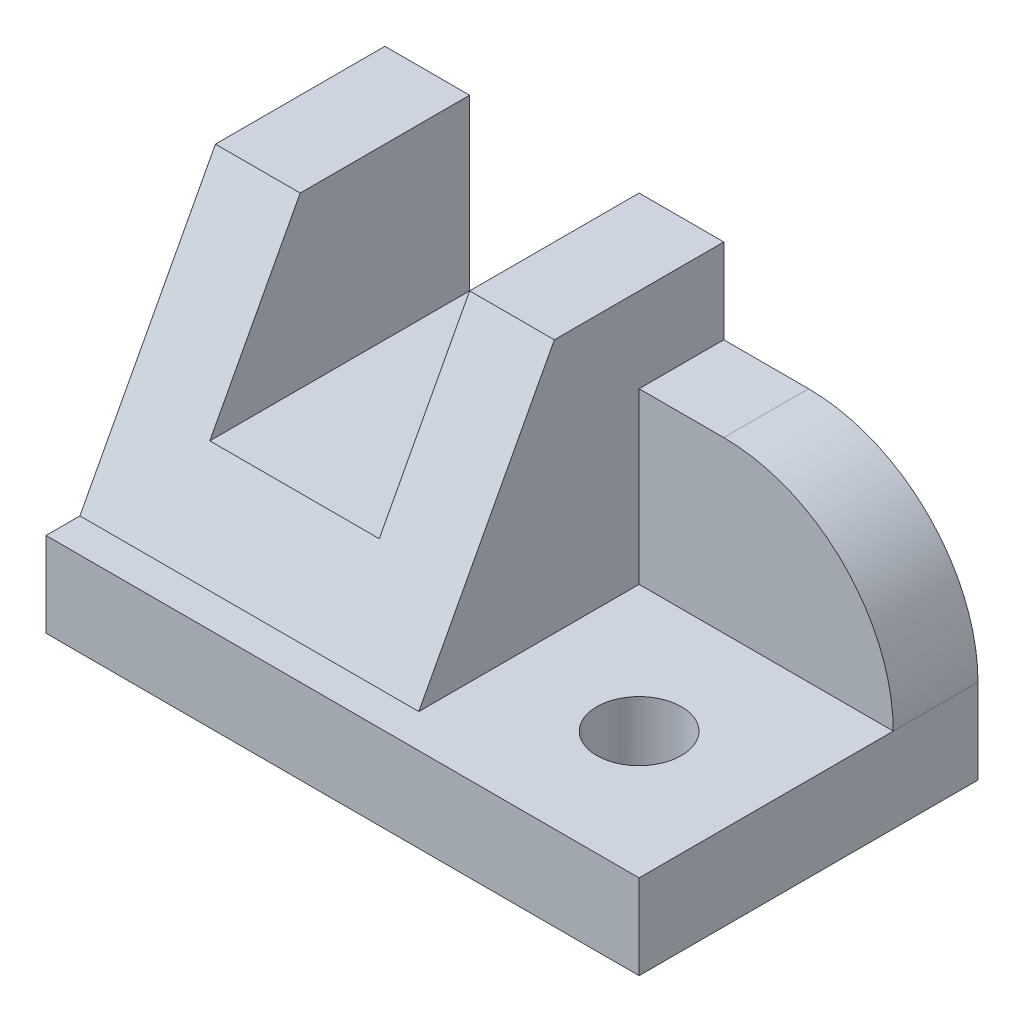
SolidWorks part; units mm, degrees
ref_plane "Front Plane" through (0, 0, 0) normal (0, 0, 1) x (1, 0, 0)
ref_plane "Top Plane" through (0, 0, 0) normal (0, 1, 0) x (1, 0, 0)
ref_plane "Right Plane" through (0, 0, 0) normal (1, 0, 0) x (0, 0, -1)
ref_plane "Plane1" through (0, 0, 0) normal (-1, 0, 0) x (0, -1, 0)
sketch "Sketch1" plane through (0, 0, 0) normal (-1, 0, 0) x (0, -1, 0)
  line L0 (-10, -4) -> (-40, -20)
  line L1 (-40, -20) -> (-10, -20)
  line L2 (-10, -20) -> (-10, -4)
  dimension "D1" = 30
  dimension "Width" = 16
extrude "Boss-Extrude1" add sketch "Sketch1" against normal blind 40
sketch "Sketch2" plane through (0, 0, -20) normal (0, 0, -1) x (-1, 0, 0)
  line L0 (-40, 40) -> (0, 40)
  line L1 (0, 40) -> (0, 10)
  line L2 (0, 10) -> (-40, 10)
  line L3 (-40, 10) -> (-40, 40)
extrude "Boss-Extrude2" add sketch "Sketch2" along normal blind 20
sketch "Sketch3" plane through (40, 0, 0) normal (1, 0, 0) x (0, 0, -1)
  line L0 (40, 10) -> (0, 10)
  line L1 (0, 10) -> (20, 40)
  line L2 (20, 40) -> (40, 40)
  line L3 (40, 40) -> (40, 10)
extrude "Boss-Extrude3" add sketch "Sketch3" along normal blind 30
sketch "Sketch4" plane through (70, 0, 0) normal (1, 0, 0) x (0, 0, -1)
  line L0 (20, 40) -> (0, 10)
  line L1 (0, 10) -> (30, 10)
  line L2 (30, 10) -> (30, 30)
  line L3 (30, 30) -> (40, 30)
  line L4 (40, 30) -> (40, 40)
  line L5 (40, 40) -> (20, 40)
extrude "Cut-Extrude1" cut sketch "Sketch4" against normal blind 30
sketch "Sketch5" plane through (0, 10, 0) normal (0, -1, 0) x (1, 0, 0)
  line L0 (70, 0) -> (70, -40)
  line L1 (70, -40) -> (0, -40)
  line L2 (0, -40) -> (0, 0)
  line L3 (0, 0) -> (70, 0)
extrude "Boss-Extrude4" add sketch "Sketch5" along normal blind 10
sketch "Sketch6" plane through (0, 0, -40) normal (0, 0, -1) x (-1, 0, 0)
  line L0 (-30, 40) -> (-30, 20)
  line L1 (-30, 20) -> (-10, 20)
  line L2 (-10, 20) -> (-10, 40)
  line L3 (-10, 40) -> (-30, 40)
extrude "Cut-Extrude2" cut sketch "Sketch6" against normal through all
hole_wizard "Ø10.0 (10) Diameter Hole1" positions "Sketch8" profile "Sketch7" hole size "Ø10.0" standard "ANSI Metric"
sketch "Sketch8" plane through (0, 0, 0) normal (0, -1, 0) x (-1, 0, 0)
  point P0 (-55, 15)
sketch "Sketch7" plane through (55, 0, -15) normal (1, 0, 0) x (0, 0, -1)
  line L0 (0, 0) -> (0, 40)
  line L1 (0, 40) -> (5, 40)
  line L2 (5, 40) -> (5, 0)
  line L5 (5, 0) -> (0, 0)
  line L11 (0, -6.35) -> (0, 107.95) construction
  dimension "Thru Hole Dia." = 10
  dimension "Thru Hole Depth" = 40
fillet "Fillet1" radius 20 1 edges at (70, 30, -35)
